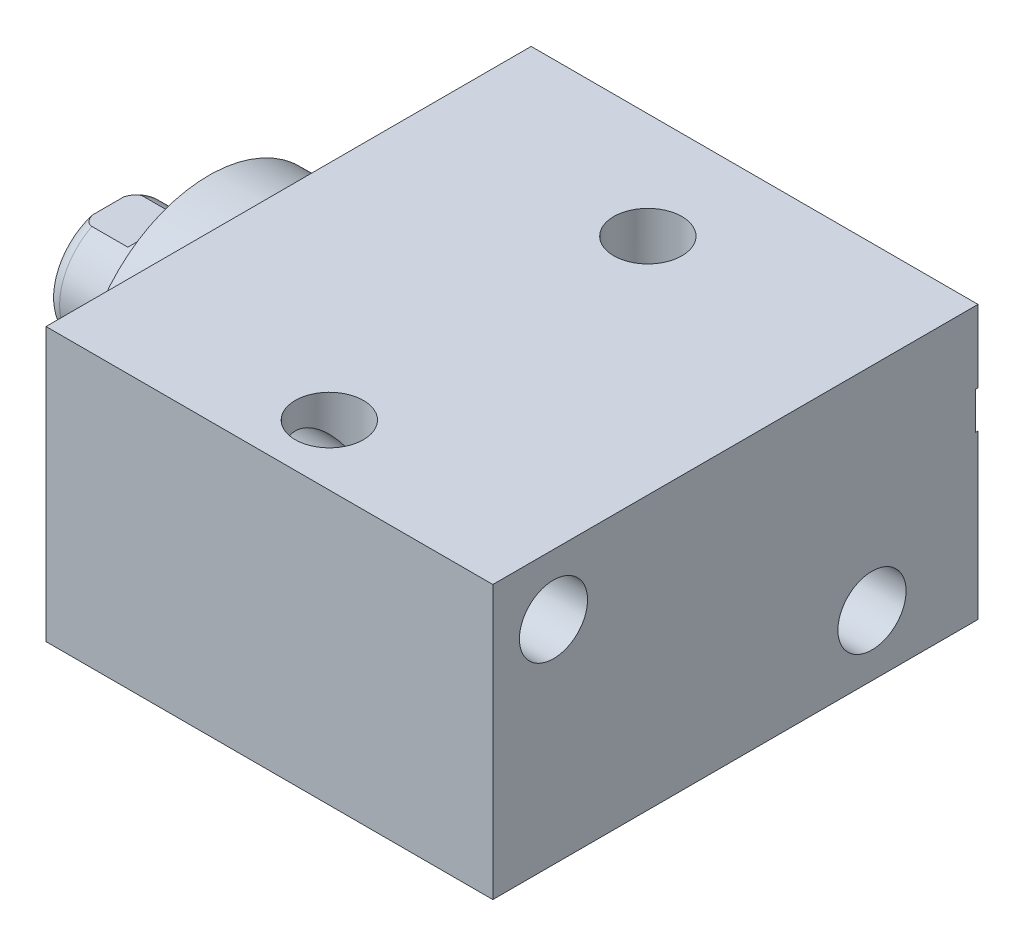
SolidWorks part; units mm, degrees
material "Alloy Steel"
ref_plane "Front Plane" through (0, 0, 0) normal (0, 0, 1) x (1, 0, 0)
ref_plane "Top Plane" through (0, 0, 0) normal (0, 1, 0) x (1, 0, 0)
ref_plane "Right Plane" through (0, 0, 0) normal (1, 0, 0) x (0, 0, -1)
ref_plane "Plane1" through (0, 0, 0) normal (1, 0, 0) x (0, 0, -1)
sketch "Sketch1" plane through (0, 0, 0) normal (1, 0, 0) x (0, 0, -1)
  line L0 (-23.0124, 14.2875) -> (27.7876, 14.2875)
  line L1 (27.7876, 14.2875) -> (27.7876, -14.2875)
  line L2 (27.7876, -14.2875) -> (-23.0124, -14.2875)
  line L3 (-23.0124, -14.2875) -> (-23.0124, 14.2875)
  line L4 (0, -24.4475) -> (0, 24.4475) construction
  dimension "D1" = 28.575
  dimension "D2" = 14.2875
  dimension "D3" = 50.8
  dimension "D4" = 23.0124
extrude "Extrude1" add sketch "Sketch1" along normal blind 46.7868
ref_plane "Plane12" through (0, 4.7625, 0) normal (0, 1, 0) x (-1, 0, 0)
sketch "S2D0002" plane through (0, 4.7625, 0) normal (0, 1, 0) x (-1, 0, 0)
  line L0 (-15.7099, -27.5336) -> (-19.05, -27.5336)
  line L1 (-15.7099, -27.5336) -> (-15.1673, -24.9809)
  line L2 (-15.1673, -24.9809) -> (-14.5034, -24.317)
  line L3 (-14.5034, -24.317) -> (-14.5034, -13.5636)
  line L4 (-14.5034, -13.5636) -> (-9.525, -13.5636)
  line L5 (-9.525, -13.5636) -> (-9.525, -27.7876)
  line L6 (-9.525, -19.1384) -> (-9.525, 0.6985) construction
  line L7 (0, -27.7876) -> (0, 23.0124) construction
  line L8 (-19.05, -27.7876) -> (-19.05, -27.5336)
  line L9 (-46.7868, -27.7876) -> (0, -27.7876) construction
  line L10 (-19.05, -27.7876) -> (-9.525, -27.7876)
  dimension "D1" = 14.224
  dimension "D2" = 9.525
  dimension "D3" = 9.9568
  dimension "D4" = 45
  dimension "D5" = 12.3698
  dimension "D6" = 12
  dimension "D7" = 2.5527
  dimension "D8" = 0.254
  dimension "D9" = 19.05
revolve "Cut-Revolve1" cut sketch "S2D0002" angle 360 about L6
ref_plane "Plane13" through (0, 4.7625, 0) normal (0, 1, 0) x (-1, 0, 0)
sketch "Sketch3" plane through (41.148, 4.7625, -25.146) normal (0, 1, 0) x (1, 0, 0)
  line L0 (2.5019, 2.3876) -> (5.842, 2.3876)
  line L1 (2.5019, 2.3876) -> (1.9593, -0.1651)
  line L2 (1.9593, -0.1651) -> (1.2954, -0.829)
  line L3 (1.2954, -0.829) -> (1.2954, -11.5824)
  line L4 (1.2954, -11.5824) -> (-3.683, -11.5824)
  line L5 (-3.683, -11.5824) -> (-3.683, 2.6416)
  line L6 (-3.683, -21.9564) -> (-3.683, 0.6985) construction
  line L7 (-41.148, 2.6416) -> (-41.148, -48.1584) construction
  line L8 (5.842, 2.6416) -> (5.842, 2.3876)
  line L9 (5.6388, 2.6416) -> (-41.148, 2.6416) construction
  line L10 (5.842, 2.6416) -> (-3.683, 2.6416)
  dimension "D1" = 14.224
  dimension "D2" = 37.465
  dimension "D3" = 9.9568
  dimension "D4" = 45
  dimension "D5" = 12
  dimension "D6" = 12.3698
  dimension "D7" = 2.5527
  dimension "D8" = 0.254
  dimension "D9" = 19.05
revolve "Cut-Revolve2" cut sketch "Sketch3" angle 360 about L6
sketch "Sketch5" plane through (0, 0, 0) normal (-1, 0, 0) x (0, 0, 1)
  circle A0 centre (0, 0) radius 13.5001
  dimension "D1" = 27.0002
extrude "Extrude2" add sketch "Sketch5" along normal blind 5.969
ref_plane "Plane5" through (0, 0, 0) normal (0, -1, 0) x (0, 0, 1)
sketch "Sketch6" plane through (0, 0, 0) normal (0, -1, 0) x (0, 0, 1)
  line L0 (0, 5.969) -> (-6.35, 5.969)
  line L1 (-6.35, 5.969) -> (-6.35, 16.51)
  line L2 (-6.35, 16.51) -> (0, 16.51)
  line L3 (0, 16.51) -> (0, 5.969)
  line L4 (0, -5.7546) -> (0, 21.1709) construction
  line L5 (13.5001, 5.969) -> (-13.5001, 5.969) construction
  line L6 (23.0124, -46.7868) -> (-27.7876, -46.7868) construction
  dimension "D1" = 63.2968
  dimension "D2" = 12.7
revolve "Revolve1" add sketch "Sketch6" angle 360 about L4
ref_plane "Plane6" through (-18.5113, 3.2639, 0) normal (0, 0, 1) x (0, 1, 0)
sketch "S2D0001" plane through (-18.5113, 3.2639, 0) normal (0, 0, 1) x (0, 1, 0)
  line L0 (-0.7112, -3.5631) -> (-0.7112, -18.0033)
  line L1 (-3.2639, -19.5371) -> (-0.7112, -18.0033)
  line L2 (0.1905, -2.0013) -> (-3.2639, -2.0013)
  line L3 (-3.2639, -2.0013) -> (-3.2639, -19.5371)
  line L4 (-0.7112, -3.5631) -> (0.1905, -2.0013)
  line L5 (-3.2639, -18.5113) -> (-3.2639, 2.765) construction
  line L6 (3.0861, -2.0013) -> (-9.6139, -2.0013) construction
  dimension "D1" = 30
  dimension "D2" = 6.9088
  dimension "D3" = 5.1054
  dimension "D4" = 16.002
  dimension "D5" = 59
revolve "Cut-Revolve4" cut sketch "S2D0001" angle 360 about L5
ref_plane "Plane7" through (0, 0, 0) normal (0, 1, 0) x (0, 0, -1)
sketch "Sketch8" plane through (0, 0, 0) normal (0, 1, 0) x (0, 0, -1)
  line L0 (-6.35, 10.1854) -> (-6.096, 10.9474)
  line L1 (-6.096, 10.9474) -> (-6.096, 15.494)
  line L2 (0, 12.6594) -> (0, 20.8178) construction
  line L3 (-6.35, 10.1854) -> (-6.35, 16.51)
  line L4 (-5.7079, 16.51) -> (-6.35, 16.51)
  line L5 (6.35, 16.51) -> (-6.35, 16.51) construction
  line L6 (-6.35, 16.51) -> (-6.35, 5.969) construction
  arc A0 (-5.7079, 16.51) -> (-6.096, 15.494) centre (-4.572, 15.494) ccw
  dimension "D2" = 1.524
  dimension "D1" = 12.192
  dimension "D3" = 1.016
  dimension "D4" = 0.762
  dimension "D5" = 5.5626
revolve "Cut-Revolve5" cut sketch "Sketch8" angle 360 about L2
ref_plane "Plane11" through (0, 0, 0) normal (0, 0, -1) x (0, -1, 0)
sketch "Sketch12" plane through (0, 0, 0) normal (0, 0, -1) x (0, -1, 0)
  line L0 (5.461, 16.51) -> (5.461, 11.7348)
  line L1 (5.461, 11.7348) -> (6.096, 11.0998)
  line L2 (-5.461, 16.51) -> (-5.461, 11.7348)
  line L3 (-5.461, 11.7348) -> (-6.096, 11.0998)
  line L4 (5.461, 16.51) -> (6.096, 16.51)
  line L5 (0, 13.7262) -> (0, 20.767) construction
  line L6 (-6.096, 11.0998) -> (-6.096, 16.51)
  line L8 (6.096, 10.9474) -> (6.096, 15.494) construction
  line L9 (6.096, 11.0998) -> (6.096, 16.51)
  line L10 (-5.461, 16.51) -> (-6.096, 16.51)
  line L12 (5.7079, 16.51) -> (-5.7079, 16.51) construction
  dimension "D1" = 10.922
  dimension "D2" = 4.7752
  dimension "D3" = 45
extrude "Cut-Extrude4" cut sketch "Sketch12" against normal mid plane 60.96
hole_wizard "Hole1" positions "Sketch15" profile "Sketch14" legacy end condition up to next
sketch "Sketch15" plane through (0, 0, 0) normal (-1, 0, 0) x (0, 0, 1)
  line L0 (0, 0) -> (-29.9914, 0) construction
  line L1 (0, 0) -> (0, 25.7648) construction
  point P0 (-16.6878, -7.9248)
  point P11 (16.6624, 7.9502)
  dimension "D1" = 7.9248
  dimension "D2" = 16.6878
  dimension "D3" = 15.875
  dimension "D4" = 33.3502
sketch "Sketch14" plane through (0, -7.9248, -16.6878) normal (0, 1, 0) x (0, 0, 1)
  line L0 (0, 0) -> (0, 46.7868)
  line L1 (0, 46.7868) -> (3.5687, 46.7868)
  line L2 (3.5687, 46.7868) -> (3.5687, 0)
  line L3 (3.5687, 0) -> (0, 0)
  line L4 (0, 110) -> (0, -10) construction
  dimension "Diameter" = 7.1374
  dimension "Depth" = 46.7868
hole_wizard "Hole2" positions "Sketch17" profile "Sketch16" legacy
sketch "Sketch17" plane through (0, 14.2875, 0) normal (0, 1, 0) x (-1, 0, 0)
  line L0 (0, 0) -> (-59.3363, 0) construction
  line L1 (0, -27.7876) -> (0, 23.0124) construction
  point P0 (-23.3172, -16.6878)
  point P9 (-23.3172, 16.6624)
  dimension "D1" = 33.3502
  dimension "D2" = 23.3172
  dimension "D3" = 16.6878
sketch "Sketch16" plane through (23.3172, 14.2875, -16.6878) normal (1, 0, 0) x (0, 0, 1)
  line L0 (0, 0) -> (0, 28.575)
  line L1 (0, 28.575) -> (3.5687, 28.575)
  line L2 (3.5687, 28.575) -> (3.5687, 0)
  line L3 (3.5687, 0) -> (0, 0)
  line L4 (0, 110) -> (0, -10) construction
  dimension "Diameter" = 7.1374
  dimension "Depth" = 28.575
